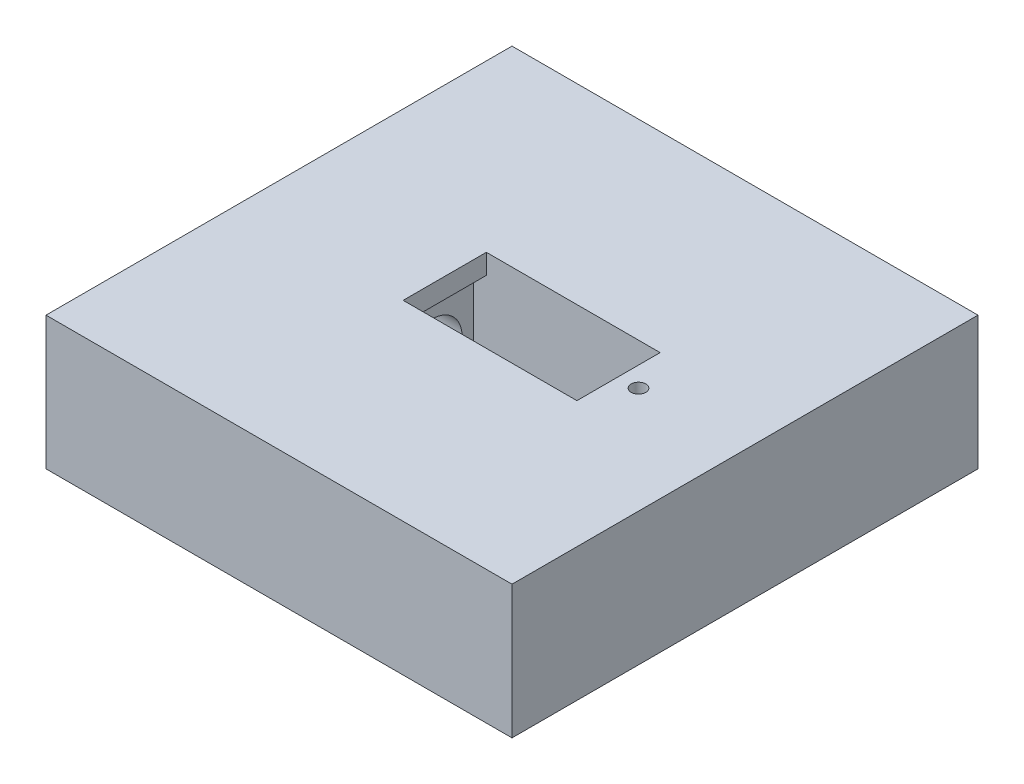
SolidWorks part; units mm, degrees
material "PLA"
ref_plane "Alzado" through (0, 0, 0) normal (0, 0, 1) x (1, 0, 0)
ref_plane "Planta" through (0, 0, 0) normal (0, 1, 0) x (1, 0, 0)
ref_plane "Vista lateral" through (0, 0, 0) normal (1, 0, 0) x (0, 0, -1)
sketch "Croquis1" plane through (0, 0, 0) normal (0, 1, 0) x (1, 0, 0)
  line L1 (-32, 32) -> (32, 32)
  line L2 (-32, 32) -> (-32, -32)
  line L3 (-32, -32) -> (32, -32)
  line L4 (32, 32) -> (32, -32)
  line L5 (-32, 32) -> (32, -32) construction
  line L6 (-32, -32) -> (32, 32) construction
  circle A0 centre (0, 0) radius 31 construction
  point P0 (0, 0)
extrude "Saliente-Extruir1" add sketch "Croquis1" along normal blind 60 contours L1 L4 L3 L2
sketch "Croquis2" plane through (0, 0, 0) normal (0, 1, 0) x (1, 0, 0)
  line L1 (-35, 35) -> (35, 35)
  line L2 (-35, 35) -> (-35, -35)
  line L3 (-35, -35) -> (35, -35)
  line L4 (35, 35) -> (35, -35)
  line L5 (-35, 35) -> (35, -35) construction
  line L6 (-35, -35) -> (35, 35) construction
  line L7 (-32, -32) -> (32, -32)
  line L8 (-32, -32) -> (-32, 32)
  line L9 (-32, 32) -> (32, 32)
  line L10 (32, -32) -> (32, 32)
  line L11 (-32, -32) -> (32, 32) construction
  line L12 (-32, 32) -> (32, -32) construction
  point P0 (0, 0)
  point P6 (0, 0)
extrude "Saliente-Extruir2" add sketch "Croquis2" along normal blind 64
sketch "Croquis3" plane through (0, 64, 0) normal (0, 1, 0) x (1, 0, 0)
  line L0 (0, 0) -> (16, 0) construction
  line L1 (0, 0) -> (0, 3.6) construction
  line L2 (0, 1.8) -> (1.9, 1.8) construction
  line L3 (1.9, 0) -> (1.9, 1.8) construction
  line L4 (1.9, 1.8) -> (1.9, 3.0578) construction
  line L5 (16, -2) -> (16, 2)
  line L6 (1.9, 3.0578) -> (16, 2)
  line L7 (1.9, -3.0578) -> (16, -2)
  line L8 (-1.9, -3.0578) -> (-16, -2)
  line L9 (-16, -2) -> (-16, 2)
  line L10 (-1.9, 3.0578) -> (-16, 2)
  circle A0 centre (0, 0) radius 3.6 construction
  arc A1 (-1.9, 3.0578) -> (1.9, 3.0578) centre (0, 0) cw
  arc A2 (-1.9, -3.0578) -> (1.9, -3.0578) centre (0, 0) ccw
sketch "Croquis4" plane through (0, 60, 0) normal (0, 1, 0) x (1, 0, 0)
  line L0 (0, 0) -> (-7, 0) construction
  line L1 (-7, 6) -> (-7, -6)
  line L3 (16, -6) -> (16, 6)
  line L5 (-7, 6) -> (-7, 6.25)
  line L6 (16, -6) -> (16, -6.25)
  line L7 (16, -6.25) -> (-7, -6.25)
  line L8 (-7, -6.25) -> (-7, -6)
  line L9 (-7, 6.25) -> (16, 6.25)
  line L10 (16, 6.25) -> (16, 6)
  point P8 (16, 0)
extrude "Cortar-Extruir1" cut sketch "Croquis4" against normal blind 21
sketch "Croquis5" plane through (0, 60, 0) normal (0, 1, 0) x (1, 0, 0)
  line L0 (16, 0) -> (19, 0) construction
  line L1 (-7, 0) -> (-9, 0) construction
  line L2 (-7, 6.25) -> (-7, -6.25) construction
  circle A0 centre (19, 0) radius 1.1
  circle A1 centre (-9, 0) radius 1.1
extrude "Cortar-Extruir2" cut sketch "Croquis5" against normal blind 10
sketch "Croquis10" plane through (-7, 0, 0) normal (1, 0, 0) x (0, 0, -1)
  line L0 (0, 39) -> (0, 44)
  line L2 (0, 39) -> (0, 60) construction
  line L3 (6.25, 39) -> (-6.25, 39) construction
  line L4 (6.25, 60) -> (-6.25, 60) construction
  circle A0 centre (0, 44) radius 4.5
extrude "Cortar-Extruir3" cut sketch "Croquis10" against normal up to next contours L2 L0 A0 | L0 L2 A0
sketch "Croquis11" plane through (0, 0, 0) normal (0, -1, 0) x (1, 0, 0)
  line L1 (-35, 35) -> (35, 35)
  line L2 (-35, 35) -> (-35, -35)
  line L3 (-35, -35) -> (35, -35)
  line L4 (35, 35) -> (35, -35)
  line L5 (-35, 35) -> (35, -35) construction
  line L6 (-35, -35) -> (35, 35) construction
  point P0 (0, 0)
extrude "Cortar-Extruir4" cut sketch "Croquis11" against normal blind 30
sketch "Croquis12" plane through (0, 30, 0) normal (0, -1, 0) x (1, 0, 0)
  line L0 (0, 0) -> (0, 22.1) construction
  line L1 (0, 22.1) -> (16, 22.1) construction
  line L2 (16, 20.2) -> (16, 24) construction
  line L3 (1.9, 0) -> (1.9, 22.1) construction
  line L4 (1.9, 22.1) -> (1.9, 25.0578) construction
  line L5 (1.9, 25.0578) -> (16, 24) construction
  line L6 (1.9, 19.1422) -> (16, 20.2) construction
  line L7 (-1.9, 25.0578) -> (-16, 24) construction
  line L8 (-16, 20.2) -> (-16, 24) construction
  line L9 (-1.9, 19.1422) -> (-16, 20.2) construction
  line L10 (0, 22.1) -> (-7, 22.1) construction
  line L11 (-7, 28.2) -> (-7, 16)
  line L12 (-7, 16) -> (16, 16)
  line L13 (16, 16) -> (16, 28.2)
  line L14 (-7, 28.2) -> (16, 28.2)
  line L15 (0, 0) -> (19.54, 0) construction
  circle A0 centre (0, 22.1) radius 3.5155 construction
  arc A1 (1.9, 25.0578) -> (-1.9, 25.0578) centre (0, 22.1) ccw construction
  arc A2 (1.9, 19.1422) -> (-1.9, 19.1422) centre (0, 22.1) cw construction
  circle A3 centre (0, 22.1) radius 24 construction
  circle A4 centre (0, -22.1) radius 24 construction
extrude "Cortar-Extruir5" cut sketch "Croquis12" against normal blind 21
sketch "Croquis13" plane through (-7, 0, 0) normal (1, 0, 0) x (0, 0, -1)
  line L0 (-22.1, 30) -> (-22.1, 46) construction
  line L2 (-28.2, 30) -> (-16, 30) construction
  circle A0 centre (-22.1, 46) radius 4.5
extrude "Cortar-Extruir6" cut sketch "Croquis13" against normal up to next
sketch "Croquis14" plane through (0, 30, 0) normal (0, -1, 0) x (1, 0, 0)
  line L0 (16, 22.1) -> (19, 22.1) construction
  line L1 (-7, 22.1) -> (-9, 22.1) construction
  circle A0 centre (19, 22.1) radius 1.1
  circle A1 centre (-9, 22.1) radius 1.1
extrude "Cortar-Extruir7" cut sketch "Croquis14" against normal blind 10
sketch "Croquis15" plane through (0, 30, 0) normal (0, -1, 0) x (1, 0, 0)
  circle A0 centre (0, -22.1) radius 3.7
extrude "Cortar-Extruir8" cut sketch "Croquis15" against normal blind 10 contours A0
sketch "Croquis16" plane through (0, 60, 0) normal (0, 1, 0) x (1, 0, 0)
  line L1 (-32, -32) -> (32, -32)
  line L2 (-32, -32) -> (-32, 32)
  line L3 (-32, 32) -> (32, 32)
  line L4 (32, -32) -> (32, 32)
  line L5 (-32, -32) -> (32, 32) construction
  line L6 (-32, 32) -> (32, -32) construction
  point P0 (0, 0)
extrude "Cortar-Extruir9" cut sketch "Croquis16" against normal blind 5
sketch "Croquis17" plane through (-7, 0, 0) normal (1, 0, 0) x (0, 0, -1)
  line L0 (6.25, 55) -> (6.25, 51.9987) construction
  line L1 (6.25, 39) -> (6.25, 55) construction
  line L2 (6.25, 51.9987) -> (-6.25, 51.9987)
  line L3 (-6.25, 39) -> (-6.25, 55) construction
  line L4 (-6.25, 51.9987) -> (-6.25, 39)
  line L5 (-6.25, 39) -> (6.25, 39)
  line L6 (6.25, 39) -> (-6.25, 39) construction
  line L7 (6.25, 39) -> (6.25, 51.9987)
extrude "Cortar-Extruir10" cut sketch "Croquis17" against normal blind 5
sketch "Croquis18" plane through (35, 0, 0) normal (1, 0, 0) x (0, 0, -1)
  line L0 (35, 64) -> (35, 30) construction
  line L1 (-35, 64) -> (35, 64)
  line L2 (-35, 64) -> (-35, 55)
  line L3 (-35, 55) -> (35, 55)
  line L4 (35, 64) -> (35, 55)
  line L5 (-35, 30) -> (-35, 35.0002)
  line L6 (-35, 64) -> (-35, 30) construction
  line L7 (-35, 35.0002) -> (35, 35.0002)
  line L8 (35, 35.0002) -> (35, 30)
  line L9 (-1.9, 30) -> (46.1, 30) construction
  line L10 (35, 30) -> (-35, 30)
extrude "Cortar-Extruir11" cut sketch "Croquis18" against normal up to next
sketch "Croquis19" plane through (-7, 0, 0) normal (1, 0, 0) x (0, 0, -1)
  line L0 (-16, 30) -> (-16, 33) construction
  line L1 (-16, 51) -> (-16, 35.0002) construction
  line L2 (-16, 51) -> (-28.2, 51)
  line L7 (-22.1, 35.0002) -> (-22.1, 38.0002) construction
  line L8 (-16, 35.0002) -> (-28.2, 35.0002) construction
  line L9 (-22.1, 38.0002) -> (-16, 38.0002)
  line L10 (-22.1, 38.0002) -> (-28.2, 38.0002)
  line L11 (-28.2, 51) -> (-28.2, 38.0002)
  line L12 (-16, 51) -> (-16, 38.0002)
  line L13 (-22.1, 35.0002) -> (-16, 35.0002) construction
  line L14 (-16, 35.0002) -> (-16, 33) construction
extrude "Cortar-Extruir13" cut sketch "Croquis19" against normal blind 5
ref_plane "Plano1" through (0, 45.0002, 0) normal (0, -1, 0) x (-1, 0, 0)
sketch "Croquis21" plane through (0, 45.0002, 0) normal (0, -1, 0) x (-1, 0, 0)
  line L1 (-40.6571, 39.9693) -> (40.8099, 39.9693)
  line L2 (-40.6571, 39.9693) -> (-40.6571, -41.4977)
  line L3 (-40.6571, -41.4977) -> (40.8099, -41.4977)
  line L4 (40.8099, 39.9693) -> (40.8099, -41.4977)
sketch "Croquis22" plane through (0, 38.0002, 0) normal (0, 1, 0) x (1, 0, 0)
  line L1 (-7, -16) -> (-10.1, -16)
  line L2 (-7, -16) -> (-7, -28.2)
  line L3 (-7, -28.2) -> (-10.1, -28.2)
  line L4 (-10.1, -16) -> (-10.1, -28.2)
sketch "Croquis23" plane through (0, 51.9987, 0) normal (0, -1, 0) x (1, 0, 0)
  line L0 (-12, -6.25) -> (-7, -6.25) construction
  line L1 (-7, 6.25) -> (-10.1, 6.25)
  line L2 (-7, 6.25) -> (-7, -6.25)
  line L3 (-7, -6.25) -> (-10.1, -6.25)
  line L4 (-10.1, 6.25) -> (-10.1, -6.25)
extrude "Cortar-Extruir16" cut sketch "Croquis23" against normal up to next
extrude "Cortar-Extruir17" cut sketch "Croquis22" against normal up to next
